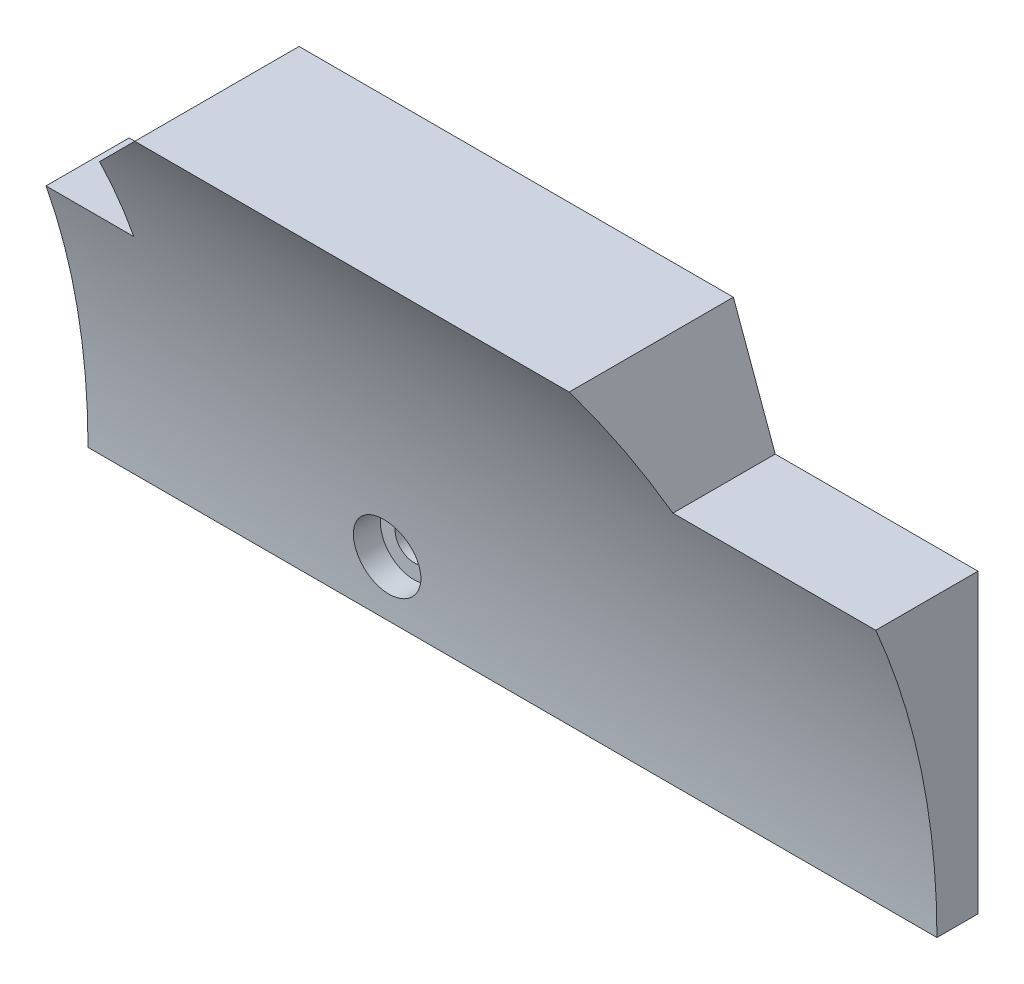
SolidWorks part; units mm, degrees
ref_plane "Ebene vorne" through (0, 0, 0) normal (0, 0, 1) x (1, 0, 0)
ref_plane "Ebene oben" through (0, 0, 0) normal (0, 1, 0) x (1, 0, 0)
ref_plane "Ebene rechts" through (0, 0, 0) normal (1, 0, 0) x (0, 0, -1)
sketch "Skizze1" plane through (0, 0, 0) normal (0, 0, 1) x (1, 0, 0)
  line L0 (53.35, 43.4251) -> (1.65, 43.4251) construction
  line L1 (53.35, 39.9251) -> (1.65, 39.9251)
  line L2 (53.35, 39.9251) -> (53.35, 46.9251)
  line L4 (1.65, 39.9251) -> (1.65, 46.9251)
  line L5 (53.35, 43.4251) -> (53.5, 43.4251) construction
  line L6 (53.5, 58) -> (53.5, -17.1274) construction
  line L7 (27.5, 27.3475) -> (27.5, 38.1252) construction
  line L8 (1.65, 43.4251) -> (1.5, 43.4251) construction
  line L9 (1.5, -64.5626) -> (1.5, 55) construction
  line L10 (53.35, 46.9251) -> (53.35, 58)
  line L11 (41, 58) -> (53.5, 58) construction
  line L12 (53.35, 58) -> (41, 58)
  line L13 (41, 58) -> (38.4522, 65)
  line L14 (38.4522, 65) -> (12, 65)
  line L15 (12, 65) -> (7, 60)
  line L16 (7, 60) -> (7, 55)
  line L17 (7, 55) -> (1.65, 55)
  line L18 (1.5, 55) -> (7, 55) construction
  line L19 (1.65, 55) -> (1.65, 46.9251)
  circle A1 centre (20, 43.4251) radius 2.05 construction
  point P8 (20, 43.4251)
  dimension "D1" = 0.15
  dimension "D2" = 7
extrude "Aufsatz-Linear austragen1" add sketch "Skizze1" along normal blind 10
sketch "Skizze2" plane through (0, 0, 10) normal (0, 0, 1) x (1, 0, 0)
  circle A0 centre (20, 43.4251) radius 1.15
  circle A1 centre (20, 43.4251) radius 1.15 construction
extrude "Schnitt-Linear austragen1" cut sketch "Skizze2" against normal through all
sketch "Skizze3" plane through (0, 0, 10) normal (0, 0, 1) x (1, 0, 0)
  circle A0 centre (20, 43.4251) radius 2.05
  circle A1 centre (20, 43.4251) radius 2.05 construction
extrude "Schnitt-Linear austragen2" cut sketch "Skizze3" against normal blind 2
sketch "Skizze4" plane through (53.35, 0, 0) normal (1, 0, 0) x (0, 0, -1)
  line L1 (-10, 65) -> (-48.1667, 39.9251)
  line L2 (-48.1667, 39.9251) -> (-2.5, 39.9251)
  line L3 (-10, 39.9251) -> (0, 39.9251) construction
  arc A0 (-10, 65) -> (-2.5, 39.9251) centre (-48.1667, 39.9251) cw
  dimension "D1" = 2.5
extrude "Schnitt-Linear austragen3" cut sketch "Skizze4" against normal through all
sketch "Skizze5" plane through (0, 0, 0) normal (0, 0, 1) x (1, 0, 0)
  circle A0 centre (20, 43.4251) radius 2.05
  circle A1 centre (20, 43.4251) radius 2.05 construction
extrude "Schnitt-Linear austragen4" cut sketch "Skizze5" along normal through all from offset 1
